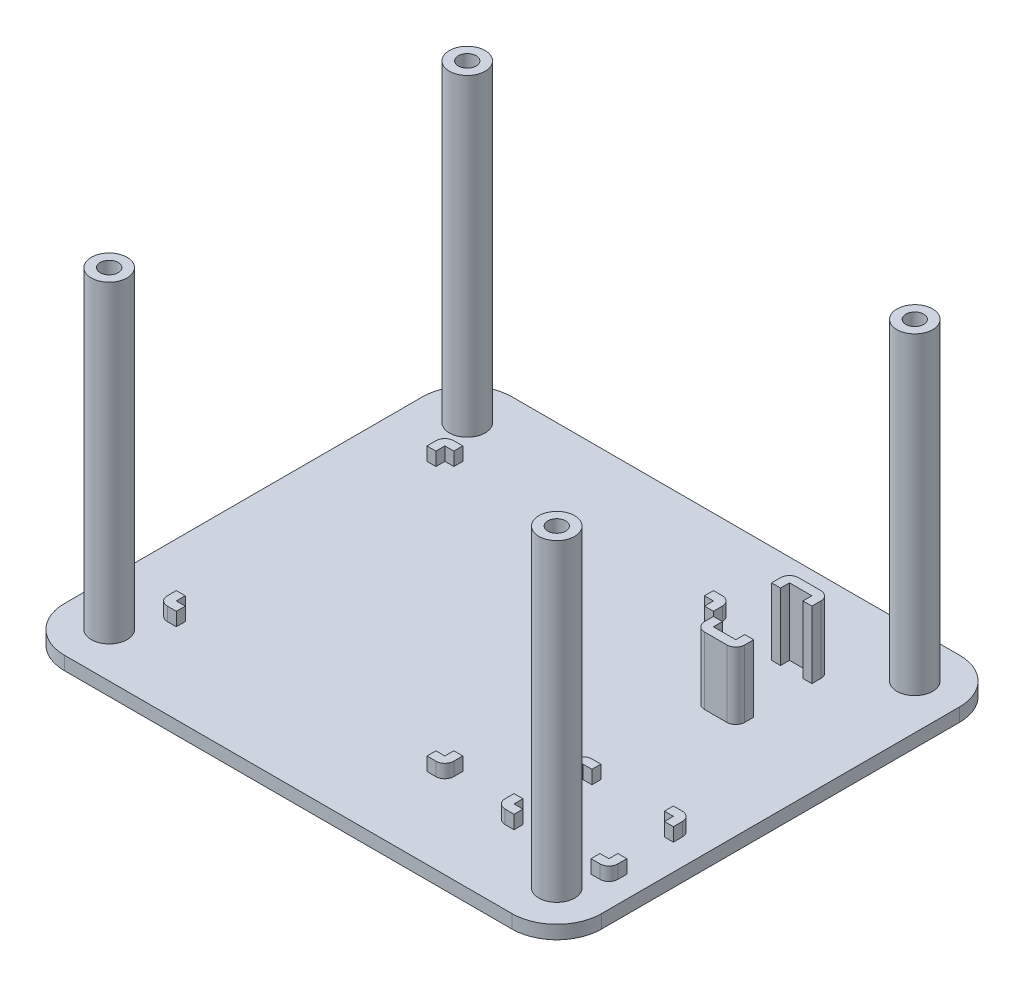
SolidWorks part; units mm, degrees
ref_plane "Plan de face" through (0, 0, 0) normal (0, 0, 1) x (1, 0, 0)
ref_plane "Plan de dessus" through (0, 0, 0) normal (0, 1, 0) x (1, 0, 0)
ref_plane "Plan de droite" through (0, 0, 0) normal (1, 0, 0) x (0, 0, -1)
sketch "Esquisse1" plane through (0, 0, 0) normal (0, 1, 0) x (1, 0, 0)
  line L1 (0, 0) -> (-120, 0)
  line L2 (0, 0) -> (0, 100)
  line L3 (0, 100) -> (-120, 100)
  line L4 (-120, 0) -> (-120, 100)
  dimension "D1" = 120
  dimension "D2" = 100
extrude "Boss.-Extru.1" add sketch "Esquisse1" along normal blind 3
sketch "Esquisse2" plane through (0, 3, 0) normal (0, 1, 0) x (1, 0, 0)
  line L0 (0, 100) -> (-120, 100) construction
  line L1 (-105, 80) -> (-45, 80)
  line L2 (-105, 80) -> (-105, 20)
  line L3 (-105, 20) -> (-45, 20)
  line L4 (-45, 80) -> (-45, 20)
  line L5 (-120, 100) -> (-120, 0) construction
  line L7 (-107, 82) -> (-103, 82)
  line L8 (-107, 82) -> (-107, 78)
  line L9 (-107, 78) -> (-103, 78)
  line L10 (-103, 82) -> (-103, 78)
  line L11 (-47, 82) -> (-43, 82)
  line L12 (-47, 82) -> (-47, 78)
  line L13 (-47, 78) -> (-43, 78)
  line L14 (-43, 82) -> (-43, 78)
  line L15 (-47, 22) -> (-43, 22)
  line L16 (-47, 22) -> (-47, 18)
  line L17 (-47, 18) -> (-43, 18)
  line L18 (-43, 22) -> (-43, 18)
  line L19 (-107, 22) -> (-103, 22)
  line L20 (-107, 22) -> (-107, 18)
  line L21 (-107, 18) -> (-103, 18)
  line L22 (-103, 22) -> (-103, 18)
  line L23 (-4.8, 16.4541) -> (-8.8, 16.4541)
  line L24 (-30, 35.8541) -> (-26, 35.8541)
  line L25 (-30, 35.8541) -> (-30, 33.8541)
  line L26 (-30, 33.8541) -> (-26, 33.8541)
  line L27 (-26, 35.8541) -> (-26, 33.8541)
  line L28 (-30, 35.8541) -> (-28, 35.8541)
  line L29 (-30, 35.8541) -> (-30, 31.8541)
  line L30 (-30, 31.8541) -> (-28, 31.8541)
  line L31 (-28, 35.8541) -> (-28, 31.8541)
  line L32 (-30, 16.4541) -> (-26, 16.4541)
  line L33 (-30, 16.4541) -> (-30, 18.4541)
  line L34 (-30, 18.4541) -> (-26, 18.4541)
  line L35 (-26, 16.4541) -> (-26, 18.4541)
  line L36 (-30, 20.4541) -> (-28, 20.4541)
  line L37 (-30, 20.4541) -> (-30, 16.4541)
  line L38 (-30, 16.4541) -> (-28, 16.4541)
  line L39 (-28, 20.4541) -> (-28, 16.4541)
  line L40 (-7.8, 35.8541) -> (-5.8, 35.8541)
  line L41 (-7.8, 35.8541) -> (-7.8, 31.8541)
  line L42 (-7.8, 31.8541) -> (-5.8, 31.8541)
  line L43 (-5.8, 35.8541) -> (-5.8, 31.8541)
  line L44 (-5.8, 35.8541) -> (-9.8, 35.8541)
  line L45 (-5.8, 35.8541) -> (-5.8, 33.8541)
  line L46 (-5.8, 33.8541) -> (-9.8, 33.8541)
  line L47 (-9.8, 35.8541) -> (-9.8, 33.8541)
  line L48 (-4.8, 20.4541) -> (-6.8, 20.4541)
  line L49 (-4.8, 20.4541) -> (-4.8, 16.4541)
  line L50 (-4.8, 16.4541) -> (-6.8, 16.4541)
  line L51 (-6.8, 20.4541) -> (-6.8, 16.4541)
  line L52 (-4.8, 16.4541) -> (-4.8, 18.4541)
  line L53 (-6.8, 16.4541) -> (-6.8, 18.4541)
  line L54 (-4.8, 18.4541) -> (-8.8, 18.4541)
  line L55 (-8.8, 16.4541) -> (-8.8, 18.4541)
  dimension "D1" = 60
  dimension "D2" = 20
  dimension "D3" = 60
  dimension "D4" = 15
  dimension "D5" = 2
  dimension "D6" = 2
  dimension "D7" = 4
  dimension "D8" = 4
  dimension "D9" = 4
  dimension "D10" = 4
  dimension "D11" = 2
  dimension "D12" = 2
  dimension "D13" = 2
  dimension "D14" = 2
  dimension "D15" = 4
  dimension "D16" = 4
  dimension "D17" = 4
  dimension "D18" = 4
  dimension "D19" = 4
  dimension "D20" = 2
  dimension "D21" = 4
  dimension "D22" = 4
  dimension "D23" = 4
  dimension "D24" = 4
  dimension "D25" = 4
  dimension "D26" = 4
  dimension "D27" = 4
  dimension "D28" = 2
  dimension "D29" = 2
  dimension "D30" = 2
  dimension "D31" = 2
  dimension "D32" = 2
  dimension "D33" = 2
  dimension "D34" = 2
  dimension "D35" = 2
  dimension "D36" = 15
  dimension "D37" = 0
  dimension "D38" = 20.2
  dimension "D39" = 21.2
  dimension "D40" = 15.4
  dimension "D41" = 15.4
extrude "Boss.-Extru.2" add sketch "Esquisse2" along normal blind 3 contours L10 L7 L8 L9 L2 L1 | L22 L3 L2 L19 L20 L21 | L18 L15 L4 L3 L16 L17 | L14 L11 L12 L1 L4 L13 | L43 L46 L41 L42 | L46 L43 L40 L41 | L44 L47 L46 L41 | L24 L31 L26 L27 | L31 L24 L25 L26 | L31 L26 L29 L30 | L39 L36 L37 L34 | L39 L34 L33 L32 | L34 L39 L32 L35 | L54 L49 L48 L51 | L49 L54 L51 L23 | L55 L23 L51 L54
sketch "Esquisse3" plane through (0, 3, 0) normal (0, 1, 0) x (1, 0, 0)
  line L1 (-28, 63) -> (-23, 63)
  line L2 (-28, 63) -> (-28, 80)
  line L3 (-28, 80) -> (-23, 80)
  line L4 (-23, 63) -> (-23, 80)
  line L5 (-30, 78) -> (-21, 78)
  line L6 (-47, 82) -> (-43, 82) construction
  line L8 (-30, 82) -> (-21, 82)
  line L9 (-30, 82) -> (-30, 61)
  line L10 (-30, 61) -> (-21, 61)
  line L11 (-21, 82) -> (-21, 61)
  line L12 (-30, 78) -> (-30, 65)
  line L13 (-30, 65) -> (-21, 65)
  line L14 (-21, 78) -> (-21, 65)
  line L15 (-29.2, 82) -> (-28.2, 82)
  line L16 (-30, 78) -> (-21, 78)
  line L17 (2.2, 61) -> (-26, 61)
  line L18 (-30, 78) -> (-30, 65)
  line L19 (-30, 65) -> (-21, 65)
  line L20 (-21, 78) -> (-21, 65)
  line L22 (-45, 80) -> (-45, 78) construction
  dimension "D1" = 2
  dimension "D2" = 17
  dimension "D3" = 5
  dimension "D4" = 2
  dimension "D5" = 2
  dimension "D6" = 2
  dimension "D7" = 2
  dimension "D8" = 15
  dimension "D9" = 4
  dimension "D10" = 4
  dimension "D11" = 13
  dimension "D12" = 4
sketch "Esquisse4" plane through (0, 3, 0) normal (0, 1, 0) x (1, 0, 0)
  line L0 (0, 0) -> (0, 100) construction
  line L1 (0, 100) -> (-120, 100) construction
  line L2 (-120, 100) -> (-120, 0) construction
  line L5 (-120, 0) -> (0, 0) construction
  circle A0 centre (-10, 90) radius 4
  circle A1 centre (-110, 90) radius 4
  circle A2 centre (-110, 10) radius 4
  circle A3 centre (-10, 10) radius 4
  dimension "D3" = 8
  dimension "D4" = 8
  dimension "D9" = 8
  dimension "D10" = 8
  dimension "D1" = 10
  dimension "D2" = 10
  dimension "D5" = 10
  dimension "D6" = 10
  dimension "D7" = 10
  dimension "D8" = 10
  dimension "D11" = 10
  dimension "D12" = 10
extrude "Boss.-Extru.4" add sketch "Esquisse4" along normal blind 70
sketch "Esquisse5" plane through (0, 73, 0) normal (0, 1, 0) x (1, 0, 0)
  circle A0 centre (-110, 90) radius 2
  circle A1 centre (-110, 10) radius 2
  circle A2 centre (-10, 90) radius 2
  circle A3 centre (-10, 10) radius 2
  dimension "D1" = 4
  dimension "D2" = 4
  dimension "D3" = 4
  dimension "D4" = 4
extrude "Enlèv. mat.-Extru.1" cut sketch "Esquisse5" against normal blind 70
fillet "Congé1" radius 10 4 edges at (0, 1.5, -100) (-120, 1.5, -100) (-120, 1.5, 0) (0, 1.5, 0)
extrude "Boss.-Extru.6" add sketch "Esquisse3" along normal blind 15 contours L11 L8 L9 L5 L2 L3 L4 | L13 L9 L10 L11 L4 L1 L2
fillet "Congé2" radius 2 12 edges at (-43, 4.5, -82) (-107, 4.5, -18) (-107, 4.5, -82) (-43, 4.5, -18) (-30, 4.5, -35.8541) (-30, 4.5, -16.4541) (-4.8, 4.5, -16.4541) (-5.8, 4.5, -35.8541) (-30, 10.5, -82) (-21, 10.5, -82) (-30, 10.5, -61) (-21, 10.5, -61)
